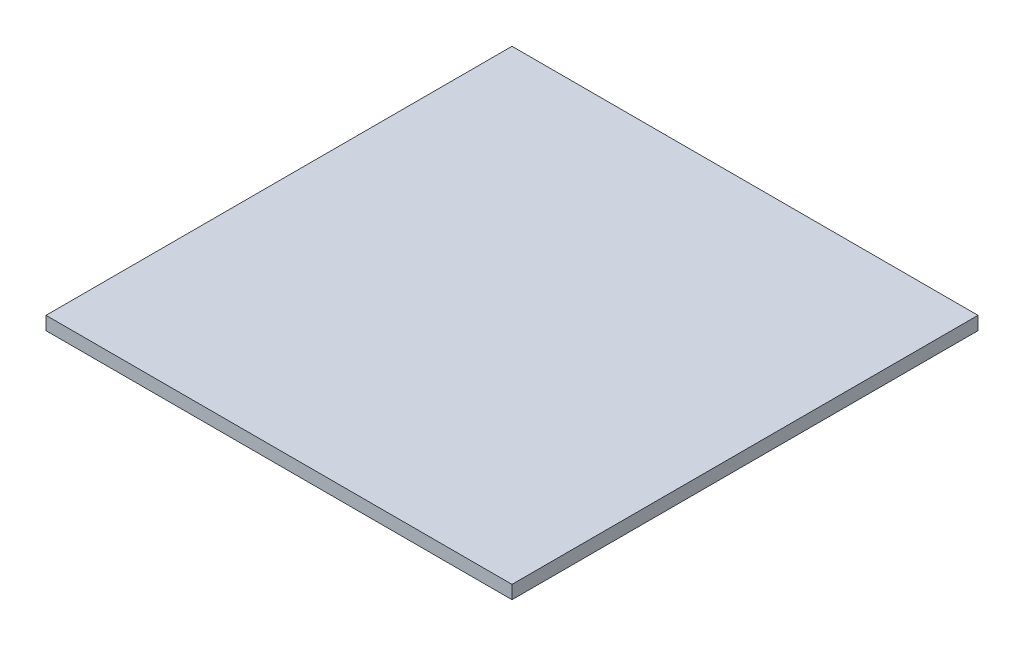
SolidWorks part; units mm, degrees
ref_plane "Face" through (0, 0, 0) normal (0, 0, 1) x (1, 0, 0)
ref_plane "Dessus" through (0, 0, 0) normal (0, 1, 0) x (1, 0, 0)
ref_plane "Droite" through (0, 0, 0) normal (1, 0, 0) x (0, 0, -1)
sketch "Esquisse1" plane through (0, 0, 0) normal (0, 1, 0) x (1, 0, 0)
  line L1 (0, 0) -> (350, 0)
  line L2 (0, 0) -> (0, 350)
  line L3 (0, 350) -> (350, 350)
  line L4 (350, 0) -> (350, 350)
  dimension "D1" = 350
  dimension "D2" = 350
extrude "Extrusion1" add sketch "Esquisse1" along normal blind 10
